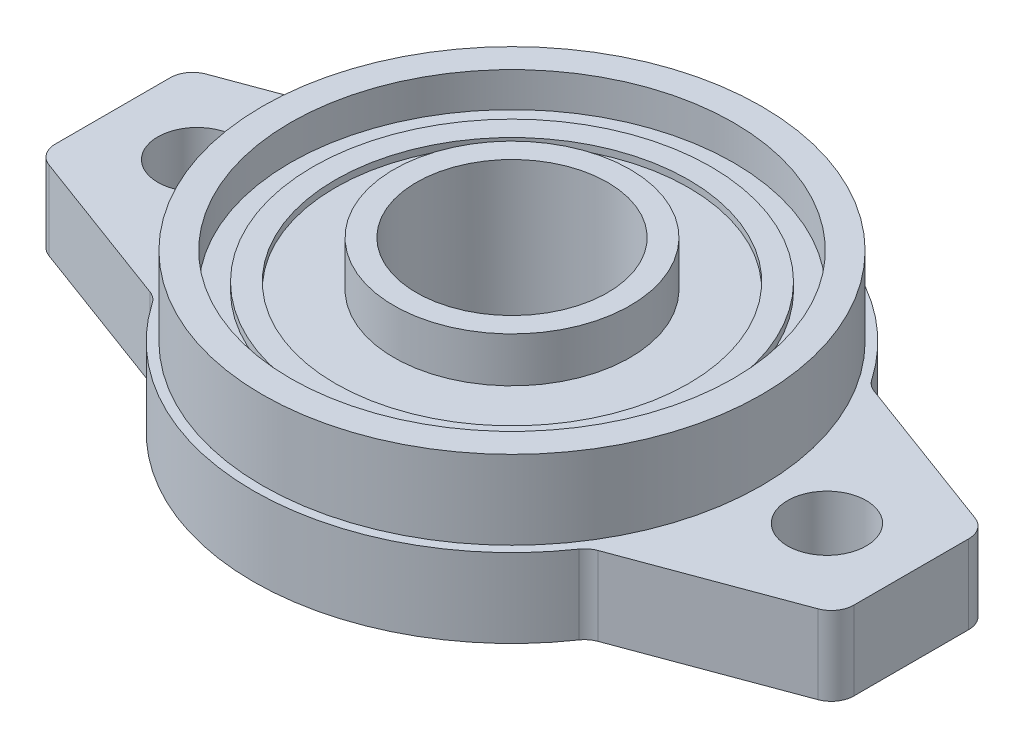
SolidWorks part; units mm, degrees
ref_plane "Front Plane" through (0, 0, 0) normal (0, 0, 1) x (1, 0, 0)
ref_plane "Top Plane" through (0, 0, 0) normal (0, 1, 0) x (1, 0, 0)
ref_plane "Right Plane" through (0, 0, 0) normal (1, 0, 0) x (0, 0, -1)
sketch "Sketch1" plane through (0, 0, 0) normal (0, 1, 0) x (1, 0, 0)
  line L0 (19.9153, 12.2745) -> (34.1949, 6.9836)
  line L1 (35.5, 5.1082) -> (35.5, -5.1082)
  line L2 (34.1949, -6.9836) -> (19.9153, -12.2745)
  line L3 (0, 0) -> (0, 16.0762) construction
  line L4 (-19.9153, 12.2745) -> (-34.1949, 6.9836)
  line L5 (-34.1949, -6.9836) -> (-19.9153, -12.2745)
  line L6 (-35.5, 5.1082) -> (-35.5, -5.1082)
  arc A0 (18.9614, 13.0179) -> (-18.9614, 13.0179) centre (0, 0) ccw
  arc A1 (-34.1949, -6.9836) -> (-35.5, -5.1082) centre (-33.5, -5.1082) cw
  arc A2 (-34.1949, 6.9836) -> (-35.5, 5.1082) centre (-33.5, 5.1082) ccw
  arc A3 (35.5, -5.1082) -> (34.1949, -6.9836) centre (33.5, -5.1082) cw
  arc A4 (34.1949, 6.9836) -> (35.5, 5.1082) centre (33.5, 5.1082) cw
  arc A5 (-18.9614, -13.0179) -> (18.9614, -13.0179) centre (0, 0) ccw
  arc A6 (-19.9153, 12.2745) -> (-18.9614, 13.0179) centre (-20.6102, 14.1499) ccw
  arc A7 (-19.9153, -12.2745) -> (-18.9614, -13.0179) centre (-20.6102, -14.1499) cw
  arc A8 (19.9153, -12.2745) -> (18.9614, -13.0179) centre (20.6102, -14.1499) ccw
  arc A9 (19.9153, 12.2745) -> (18.9614, 13.0179) centre (20.6102, 14.1499) cw
  circle A10 centre (28, 0) radius 3.5
  circle A11 centre (-28, 0) radius 3.5
  circle A12 centre (0, 0) radius 8.5
  point P13 (35.5, 0)
  point P16 (-35.5, -6.5)
  point P19 (-35.5, 6.5)
  point P22 (35.5, -6.5)
  point P25 (35.5, 6.5)
  point P27 (-19.3067, 12.5)
  point P30 (-19.3067, -12.5)
  point P33 (19.3067, -12.5)
  point P36 (19.3067, 12.5)
  dimension "D1" = 46
  dimension "D5" = 2
  dimension "D6" = 2
  dimension "D8" = 7
  dimension "D9" = 17
  dimension "D2" = 71
  dimension "D3" = 25
  dimension "D4" = 13
  dimension "D7" = 56
extrude "Boss-Extrude1" add sketch "Sketch1" along normal blind 7
sketch "Sketch2" plane through (0, 0, 0) normal (0, 0, 1) x (1, 0, 0)
  line L0 (0, 0) -> (0, 26.6602) construction
  line L1 (-8.5, 15) -> (-8.5, 7)
  line L3 (-8.5, 15) -> (-10.5, 15)
  line L4 (-10.5, 15) -> (-10.5, 11)
  line L14 (18.9614, 7) -> (-18.9614, 7) construction
  line L15 (-10.5, 11) -> (-15.7, 11)
  line L16 (-15.7, 11) -> (-15.7, 11.6)
  line L17 (-15.7, 11.6) -> (-17.7, 11.6)
  line L18 (-17.7, 11.6) -> (-17.7, 10.9183)
  line L19 (-17.7, 10.9183) -> (-19.7, 10.9183)
  line L20 (-19.7, 10.9183) -> (-19.7, 14)
  line L21 (-19.7, 14) -> (-22.2, 14)
  line L22 (-22.2, 14) -> (-22.2, 7)
  line L24 (-22.2, 7) -> (-8.5, 7)
  dimension "D1" = 8
  dimension "D2" = 8.5
  dimension "D3" = 2
  dimension "D4" = 4
  dimension "D5" = 5.2
  dimension "D6" = 2
  dimension "D7" = 2
  dimension "D8" = 2.5
  dimension "D9" = 0.6
  dimension "D10" = 7
  dimension "D11" = 3.9183
revolve "Revolve1" add sketch "Sketch2" angle 360 about L0
